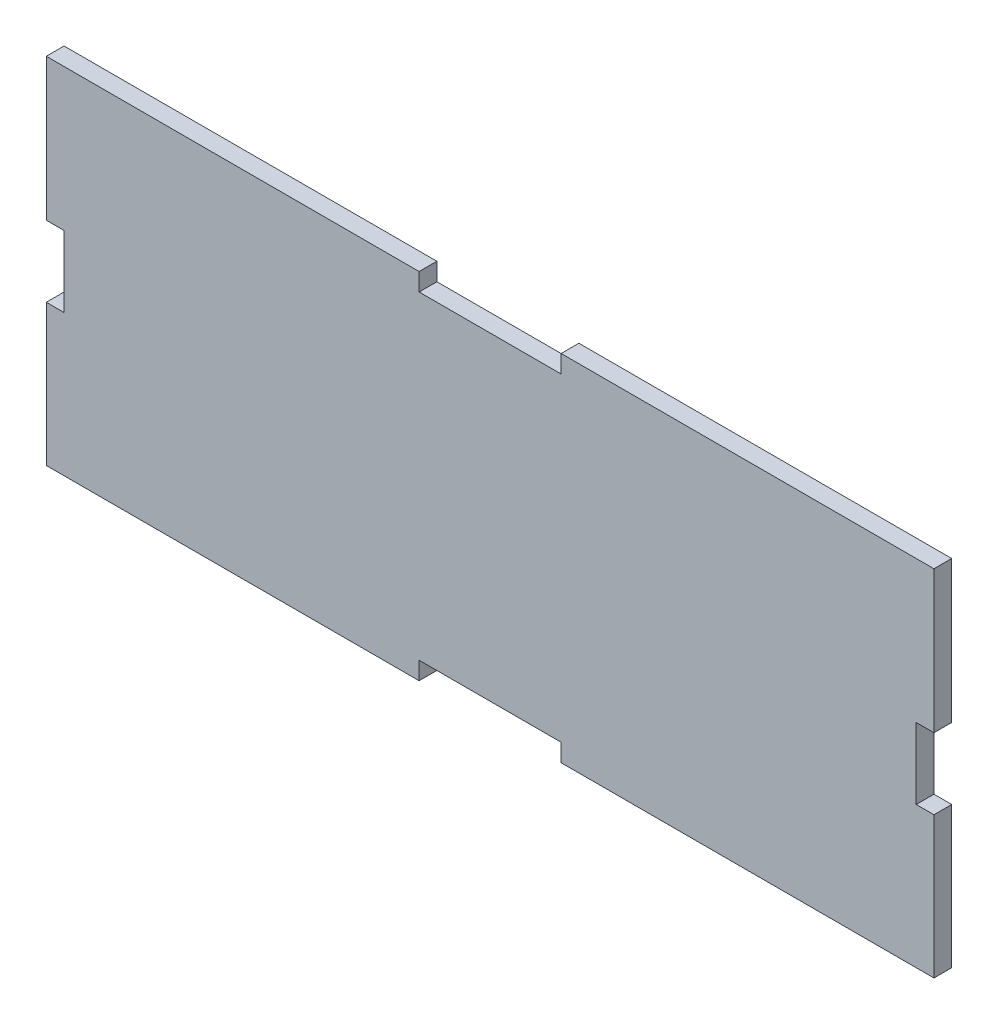
SolidWorks part; units mm, degrees
ref_plane "Plan de face" through (0, 0, 0) normal (0, 0, 1) x (1, 0, 0)
ref_plane "Plan de dessus" through (0, 0, 0) normal (0, 1, 0) x (1, 0, 0)
ref_plane "Plan de droite" through (0, 0, 0) normal (1, 0, 0) x (0, 0, -1)
sketch "Esquisse1" plane through (0, 0, 0) normal (0, 0, 1) x (1, 0, 0)
  line L0 (125, 17.6201) -> (125, -94.6337) construction
  line L6 (105, 12.4393) -> (105, 17.4393)
  line L7 (0, -32.5607) -> (276.5026, -32.5607) construction
  line L9 (5, -22.5607) -> (0, -22.5607)
  line L10 (0, -42.5607) -> (5, -42.5607)
  line L13 (105, -77.3799) -> (105, -82.3799)
  line L14 (145, -77.3799) -> (145, -82.3799)
  line L17 (245, -42.5607) -> (250, -42.5607)
  line L18 (250, -22.5607) -> (245, -22.5607)
  line L21 (145, 12.4393) -> (145, 17.4393)
  line L23 (5, -22.5607) -> (5, -42.5607)
  line L24 (0, 17.4393) -> (105, 17.4393)
  line L25 (0, 17.4393) -> (0, -22.5607)
  line L26 (0, -82.3799) -> (105, -82.3799)
  line L27 (250, 17.4393) -> (250, -22.5607)
  line L28 (145, -82.3799) -> (250, -82.3799)
  line L29 (145, 17.4393) -> (250, 17.4393)
  line L30 (250, -42.5607) -> (250, -82.3799)
  line L31 (0, -42.5607) -> (0, -82.3799)
  line L32 (105, 12.4393) -> (145, 12.4393)
  line L33 (105, -77.3799) -> (145, -77.3799)
  line L34 (245, -42.5607) -> (245, -22.5607)
  dimension "D2" = 20
  dimension "D9" = 20
  dimension "D10" = 10
  dimension "D11" = 10
extrude "Boss.-Extru.1" add sketch "Esquisse1" along normal blind 5
